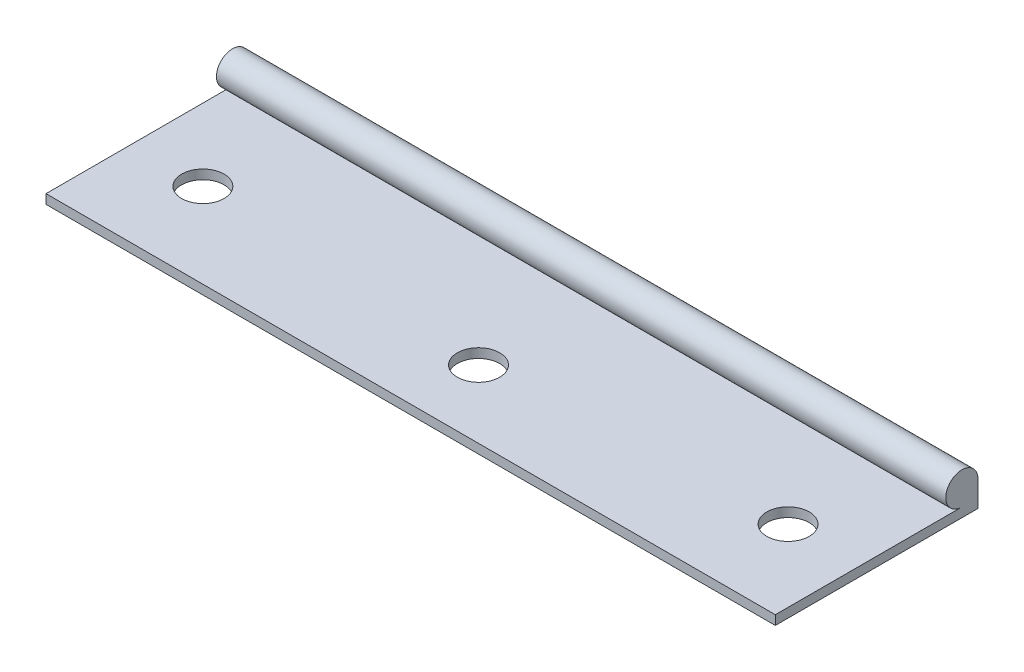
SolidWorks part; units mm, degrees
ref_plane "Front" through (0, 0, 0) normal (0, 0, 1) x (1, 0, 0)
ref_plane "Top" through (0, 0, 0) normal (0, 1, 0) x (1, 0, 0)
ref_plane "Right" through (0, 0, 0) normal (1, 0, 0) x (0, 0, -1)
sketch "草图1" plane through (0, 0, 0) normal (1, 0, 0) x (0, 0, -1)
  line L0 (0, 0) -> (0, 1.1)
  line L1 (0, 1.1) -> (19, 1.1)
  line L2 (0, 0) -> (19, 0)
  line L3 (19, 0) -> (19, 10.8121) construction
  line L4 (19, 1.1) -> (22, 1.1)
  line L5 (19, 0) -> (23.9, 0)
  line L6 (23.9, 0) -> (23.9, 3)
  circle A0 centre (22, 3) radius 3 construction
  circle A1 centre (22, 3) radius 1.9
  dimension "D3" = 6
  dimension "D1" = 1.1
  dimension "D2" = 19
extrude "凸台-拉伸1" add sketch "草图1" along normal blind 86 contours A1 | A1 L4 L1 L0 L2 L5 L6
sketch "草图2" plane through (0, 1.1, 0) normal (0, 1, 0) x (1, 0, 0)
  line L0 (0, 10) -> (86, 10) construction
  line L1 (0, 0) -> (0, 22) construction
  line L2 (86, 0) -> (86, 22) construction
  line L3 (86, 0) -> (0, 0) construction
  line L4 (43, 10) -> (43, -0.9364) construction
  line L5 (86, 0) -> (0, 0) construction
  circle A0 centre (8.5, 10) radius 2.5
  circle A1 centre (77.5, 10) radius 2.5
  circle A2 centre (43, 8) radius 2.5
  dimension "D1" = 5
  dimension "D2" = 5
  dimension "D6" = 8
  dimension "D3" = 8.5
  dimension "D4" = 10
  dimension "D5" = 8.5
extrude "切除-拉伸1" cut sketch "草图2" against normal through all
